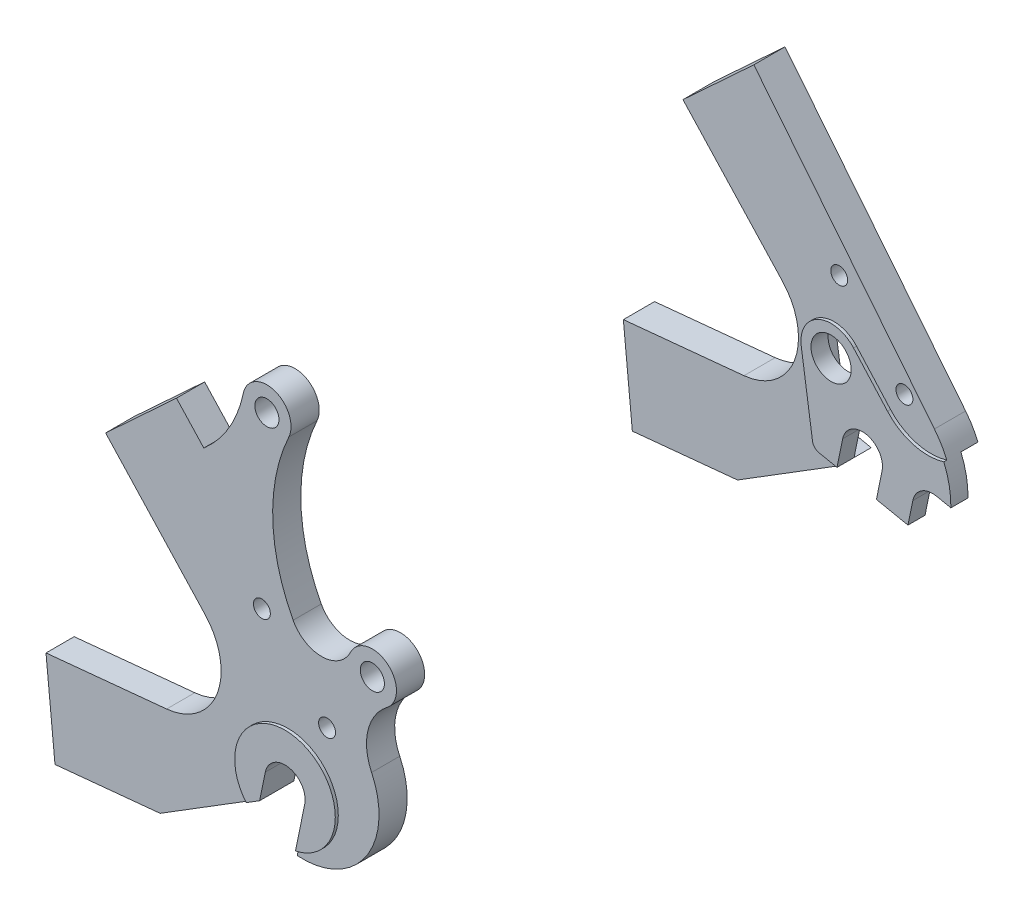
SolidWorks part; units mm, degrees
ref_plane "Plan de face" through (0, 0, 0) normal (0, 0, 1) x (1, 0, 0)
ref_plane "Plan de dessus" through (0, 0, 0) normal (0, 1, 0) x (1, 0, 0)
ref_plane "Plan de droite" through (0, 0, 0) normal (1, 0, 0) x (0, 0, -1)
sketch "Esquisse1" plane through (0, 0, 0) normal (0, 0, 1) x (1, 0, 0)
  line L0 (0, 0) -> (-619.8563, 51.5961) construction
  line L1 (0, 0) -> (-389.1874, 545.3743) construction
  line L2 (0, 0) -> (457.0972, 51.5961) construction
  line L3 (0, 0) -> (163.4516, 525.8703) construction
  line L4 (132.0822, 424.9462) -> (457.0972, 51.5961) construction
  line L5 (-489.2424, 277.5909) -> (-356.2649, 633.487) construction
  line L6 (-379.7372, 570.6665) -> (-22.8665, 389.9919) construction
  line L7 (-22.8665, 389.9919) -> (129.7077, 417.3067) construction
  line L8 (132.0822, 424.9462) -> (574.0462, -52.7114) construction
  line L9 (0, 0) -> (716.0918, 69.8126) construction
  circle A0 centre (457.0972, 51.5961) radius 15 construction
  circle A1 centre (457.0972, 51.5961) radius 7 construction
  dimension "D13" = 30
  dimension "D14" = 14
  dimension "D1" = 622
  dimension "D2" = 670
  dimension "D3" = 545
  dimension "D4" = 460
  dimension "D5" = 445
  dimension "D6" = 495
  dimension "D7" = 535
  dimension "D8" = 27
  dimension "D9" = 8
  dimension "D10" = 155
  dimension "D11" = 400
  dimension "D12" = 56
ref_plane "Plan1" through (0, 0, 71.75) normal (0, 0, 1) x (1, 0, 0)
sketch "Esquisse24" plane through (0, 0, 71.75) normal (0, 0, 1) x (1, 0, 0)
  line L0 (461.9958, 50.5942) -> (459.3907, 37.8579)
  line L1 (452.1986, 52.5981) -> (450.7959, 45.7401)
  line L2 (450.7959, 45.7401) -> (425.3126, 29.9097)
  line L3 (425.3126, 29.9097) -> (399.1754, 27.3616)
  line L4 (399.1754, 27.3616) -> (396.9437, 50.253)
  line L5 (396.9437, 50.253) -> (426.9282, 53.1763)
  line L6 (436.4827, 78.2927) -> (411.7587, 105.0135)
  line L7 (411.7587, 105.0135) -> (429.3747, 121.3131)
  line L8 (405.3822, 129.5741) -> (432.0178, 100.7874) construction
  line L9 (471.0315, 119.7214) -> (448.352, 8.8407) construction
  line L10 (0, 0) -> (457.0972, 51.5961) construction
  line L11 (366.5206, 35.7325) -> (418.0531, 40.7565) construction
  line L12 (132.0822, 424.9462) -> (574.0462, -52.7114) construction
  line L13 (429.3747, 121.3131) -> (436.1662, 113.9732)
  line L14 (0, 0) -> (716.0918, 69.8126) construction
  arc A0 (461.9958, 50.5942) -> (452.1986, 52.5981) centre (457.0972, 51.5961) ccw
  arc A1 (459.3907, 37.8579) -> (477.8671, 64.9867) centre (460.7157, 56.8116) ccw
  arc A2 (481.7003, 80.9029) -> (472.6469, 88.2693) centre (478.0533, 85.6673) ccw
  arc A3 (481.7003, 80.9029) -> (477.8671, 64.9867) centre (489.6022, 70.5801) ccw
  arc A4 (457.2988, 126.9135) -> (445.9713, 130.6341) centre (451.8471, 129.4192) ccw
  arc A5 (458.3628, 88.0055) -> (472.6469, 88.2693) centre (465.4383, 91.7387) ccw
  arc A6 (436.4827, 78.2927) -> (426.9282, 53.1763) centre (425.4727, 68.1055) cw
  arc A9 (457.2988, 126.9135) -> (458.3628, 88.0055) centre (497.2782, 108.5382) ccw
  arc A10 (436.1662, 113.9732) -> (445.9713, 130.6341) centre (416.5927, 136.7081) ccw
  dimension "D1" = 10
  dimension "D2" = 15
  dimension "D3" = 19
  dimension "D5" = 6
  dimension "D6" = 8
  dimension "D8" = 23
  dimension "D15" = 12
  dimension "D18" = 51
  dimension "D19" = 13
  dimension "D20" = 44
  dimension "D22" = 21.5
  dimension "D23" = 28
  dimension "D24" = 30
  dimension "D4" = 72
  dimension "D7" = 40
  dimension "D9" = 30
  dimension "D10" = 60
  dimension "D11" = 7
  dimension "D12" = 13
  dimension "D13" = 24
  dimension "D14" = 70
  dimension "D16" = 78
  dimension "D17" = 34
  dimension "D21" = 10
extrude "Extrusion8" add sketch "Esquisse24" along normal mid plane 7
sketch "Esquisse25" plane through (0, 0, 71.75) normal (0, 0, 1) x (1, 0, 0)
  line L0 (132.0822, 424.9462) -> (574.0462, -52.7114) construction
  line L1 (450.5982, 86.5961) -> (466.8019, 69.0838) construction
  circle A0 centre (466.8019, 69.0838) radius 2.1
  circle A1 centre (451.8471, 129.4192) radius 3
  circle A2 centre (450.5982, 86.5961) radius 2.1
  circle A3 centre (478.0533, 85.6673) radius 3
  arc A6 (481.7003, 80.9029) -> (472.6469, 88.2693) centre (478.0533, 85.6673) ccw construction
  arc A7 (457.2988, 126.9135) -> (445.9713, 130.6341) centre (451.8471, 129.4192) ccw construction
  dimension "D1" = 6
  dimension "D2" = 4.2
  dimension "D3" = 20
  dimension "D4" = 35
  dimension "D5" = 4
extrude "Enlèv. mat.-Extru.7" cut sketch "Esquisse25" against normal through all and the other way through all
sketch "Esquisse26" plane through (0, 0, 71.75) normal (0, 0, 1) x (1, 0, 0)
  line L3 (461.9958, 50.5942) -> (459.7, 39.3701)
  line L4 (450.7959, 45.7401) -> (452.1986, 52.5981)
  line L5 (447.4423, 43.6568) -> (450.7959, 45.7401)
  line L6 (450.7959, 45.7401) -> (452.1986, 52.5981) construction
  line L7 (425.3126, 29.9097) -> (450.7959, 45.7401) construction
  line L8 (461.9958, 50.5942) -> (459.3907, 37.8579) construction
  arc A0 (459.7, 39.3701) -> (447.4423, 43.6568) centre (457.0972, 51.5961) ccw
  arc A2 (461.9958, 50.5942) -> (452.1986, 52.5981) centre (457.0972, 51.5961) ccw
  arc A3 (461.9958, 50.5942) -> (452.1986, 52.5981) centre (457.0972, 51.5961) ccw construction
  dimension "D1" = 25
extrude "Extrusion9" add sketch "Esquisse26" along normal mid plane 8.5
ref_plane "Plan2" through (0, 0, -71.75) normal (0, 0, 1) x (1, 0, 0)
sketch "Esquisse27" plane through (0, 0, -71.75) normal (0, 0, 1) x (1, 0, 0)
  line L0 (396.9437, 50.253) -> (399.1754, 27.3616) construction
  line L1 (426.9282, 53.1763) -> (396.9437, 50.253) construction
  line L2 (399.1754, 27.3616) -> (425.3126, 29.9097) construction
  line L3 (425.3126, 29.9097) -> (447.4423, 43.6568) construction
  line L4 (461.9958, 50.5942) -> (459.7, 39.3701) construction
  line L5 (450.7959, 45.7401) -> (452.1986, 52.5981) construction
  line L8 (429.3747, 121.3131) -> (474.2579, 65.3624)
  line L9 (411.7587, 105.0135) -> (436.4827, 78.2927)
  line L10 (426.9282, 53.1763) -> (396.9437, 50.253)
  line L11 (396.9437, 50.253) -> (399.1754, 27.3616)
  line L12 (399.1754, 27.3616) -> (425.3126, 29.9097)
  line L13 (425.3126, 29.9097) -> (450.7959, 45.7401)
  line L14 (450.7959, 45.7401) -> (452.1986, 52.5981)
  line L15 (461.9958, 50.5942) -> (460.593, 43.7362)
  line L16 (429.3747, 121.3131) -> (411.7587, 105.0135)
  line L17 (460.593, 43.7362) -> (468.4308, 42.133)
  line L18 (468.4308, 42.133) -> (469.6331, 48.0113)
  line L19 (475.5336, 51.908) -> (479.0932, 51.1799)
  line L20 (411.7587, 105.0135) -> (436.4827, 78.2927) construction
  line L21 (429.3747, 121.3131) -> (411.7587, 105.0135) construction
  arc A0 (426.9282, 53.1763) -> (436.4827, 78.2927) centre (425.4727, 68.1055) ccw construction
  arc A1 (461.9958, 50.5942) -> (452.1986, 52.5981) centre (457.0972, 51.5961) ccw construction
  arc A7 (479.0932, 51.1799) -> (474.2579, 65.3624) centre (457.0972, 51.5961) ccw
  arc A8 (469.6331, 48.0113) -> (475.5336, 51.908) centre (474.5317, 47.0094) cw
  arc A12 (426.9282, 53.1763) -> (436.4827, 78.2927) centre (425.4727, 68.1055) ccw
  arc A13 (461.9958, 50.5942) -> (452.1986, 52.5981) centre (457.0972, 51.5961) ccw
  dimension "D1" = 22
  dimension "D3" = 5
  dimension "D2" = 8
  dimension "D4" = 11
extrude "Extrusion10" add sketch "Esquisse27" along normal blind 3.5 and the other way blind 4.25
sketch "Esquisse31" plane through (0, 0, -71.75) normal (0, 0, 1) x (1, 0, 0)
  line L0 (459.263, 62.1848) -> (453.0724, 31.9188) construction
  line L1 (450.7959, 45.7401) -> (452.1986, 52.5981) construction
  line L2 (461.9958, 50.5942) -> (460.593, 43.7362) construction
  line L3 (468.4935, 49.2651) -> (447.0445, 53.6523) construction
  line L4 (444.7134, 48.3297) -> (441.9061, 67.4041)
  line L5 (468.4308, 42.133) -> (446.2913, 46.6614)
  line L6 (460.593, 43.7362) -> (468.4308, 42.133) construction
  line L7 (463.3461, 64.1064) -> (454.9071, 73.5065)
  line L8 (468.4308, 42.133) -> (469.6331, 48.0113)
  line L9 (468.4308, 42.133) -> (469.6331, 48.0113) construction
  line L10 (475.5336, 51.908) -> (479.0932, 51.1799) construction
  line L11 (475.5336, 51.908) -> (479.0932, 51.1799)
  arc A0 (454.9071, 73.5065) -> (441.9061, 67.4041) centre (449.3262, 68.4962) ccw
  arc A1 (446.2913, 46.6614) -> (444.7134, 48.3297) centre (446.6921, 48.6209) cw
  arc A2 (475.5336, 51.908) -> (469.6331, 48.0113) centre (474.5317, 47.0094) ccw construction
  arc A3 (479.0932, 51.1799) -> (474.2579, 65.3624) centre (457.0972, 51.5961) ccw construction
  arc A4 (475.5336, 51.908) -> (469.6331, 48.0113) centre (474.5317, 47.0094) ccw
  arc A5 (479.0932, 51.1799) -> (477.3387, 60.2147) centre (457.0972, 51.5961) ccw
  arc A6 (463.3461, 64.1064) -> (477.3387, 60.2147) centre (473.3918, 73.1249) ccw
  arc A7 (461.9958, 50.5942) -> (452.1986, 52.5981) centre (457.0972, 51.5961) ccw construction
  point P22 (444.9176, 46.9424)
  dimension "D1" = 24
  dimension "D4" = 7.5
  dimension "D5" = 2
  dimension "D6" = 19.5
  dimension "D7" = 13.5
  dimension "D8" = 8.5
  dimension "D2" = 11
  dimension "D3" = 15
extrude "Enlèv. mat.-Extru.8" cut sketch "Esquisse31" against normal through all
sketch "Esquisse32" plane through (0, 0, -71.75) normal (0, 0, 1) x (1, 0, 0)
  line L8 (446.2913, 46.6614) -> (450.7959, 45.7401)
  line L9 (441.9061, 67.4041) -> (444.7134, 48.3297)
  line L10 (463.3461, 64.1064) -> (454.9071, 73.5065)
  line L11 (475.5336, 51.908) -> (479.0932, 51.1799)
  line L12 (468.4308, 42.133) -> (469.6331, 48.0113)
  line L13 (460.593, 43.7362) -> (468.4308, 42.133)
  line L14 (461.9958, 50.5942) -> (460.593, 43.7362)
  line L15 (450.7959, 45.7401) -> (452.1986, 52.5981)
  line L16 (446.2913, 46.6614) -> (450.7959, 45.7401)
  line L17 (441.9061, 67.4041) -> (444.7134, 48.3297)
  line L18 (463.3461, 64.1064) -> (454.9071, 73.5065)
  line L19 (475.5336, 51.908) -> (479.0932, 51.1799)
  line L20 (468.4308, 42.133) -> (469.6331, 48.0113)
  line L21 (460.593, 43.7362) -> (468.4308, 42.133)
  line L22 (461.9958, 50.5942) -> (460.593, 43.7362)
  line L23 (450.7959, 45.7401) -> (452.1986, 52.5981)
  arc A6 (444.7134, 48.3297) -> (446.2913, 46.6614) centre (446.6921, 48.6209) ccw
  arc A7 (454.9071, 73.5065) -> (441.9061, 67.4041) centre (449.3262, 68.4962) ccw
  arc A8 (463.3461, 64.1064) -> (477.3387, 60.2147) centre (473.3918, 73.1249) ccw
  arc A9 (479.0932, 51.1799) -> (477.3387, 60.2147) centre (457.0972, 51.5961) ccw
  arc A10 (475.5336, 51.908) -> (469.6331, 48.0113) centre (474.5317, 47.0094) ccw
  arc A11 (461.9958, 50.5942) -> (452.1986, 52.5981) centre (457.0972, 51.5961) ccw
  arc A12 (444.7134, 48.3297) -> (446.2913, 46.6614) centre (446.6921, 48.6209) ccw
  arc A13 (454.9071, 73.5065) -> (441.9061, 67.4041) centre (449.3262, 68.4962) ccw
  arc A14 (463.3461, 64.1064) -> (477.3387, 60.2147) centre (473.3918, 73.1249) ccw
  arc A15 (479.0932, 51.1799) -> (477.3387, 60.2147) centre (457.0972, 51.5961) ccw
  arc A16 (475.5336, 51.908) -> (469.6331, 48.0113) centre (474.5317, 47.0094) ccw
  arc A17 (461.9958, 50.5942) -> (452.1986, 52.5981) centre (457.0972, 51.5961) ccw
  dimension "D1" = 0
extrude "Extrusion11" add sketch "Esquisse32" along normal blind 4.25
sketch "Esquisse29" plane through (0, 0, -71.75) normal (0, 0, 1) x (1, 0, 0)
  circle A0 centre (449.3262, 68.4962) radius 5
  circle A4 centre (466.8019, 69.0838) radius 2.1
  circle A5 centre (450.5982, 86.5961) radius 2.1
  arc A6 (454.9071, 73.5065) -> (441.9061, 67.4041) centre (449.3262, 68.4962) ccw construction
  circle A7 centre (450.5982, 86.5961) radius 2.1 construction
  circle A8 centre (466.8019, 69.0838) radius 2.1 construction
  dimension "D1" = 10
extrude "Enlèv. mat.-Extru.9" cut sketch "Esquisse29" against normal through all and the other way up to next
